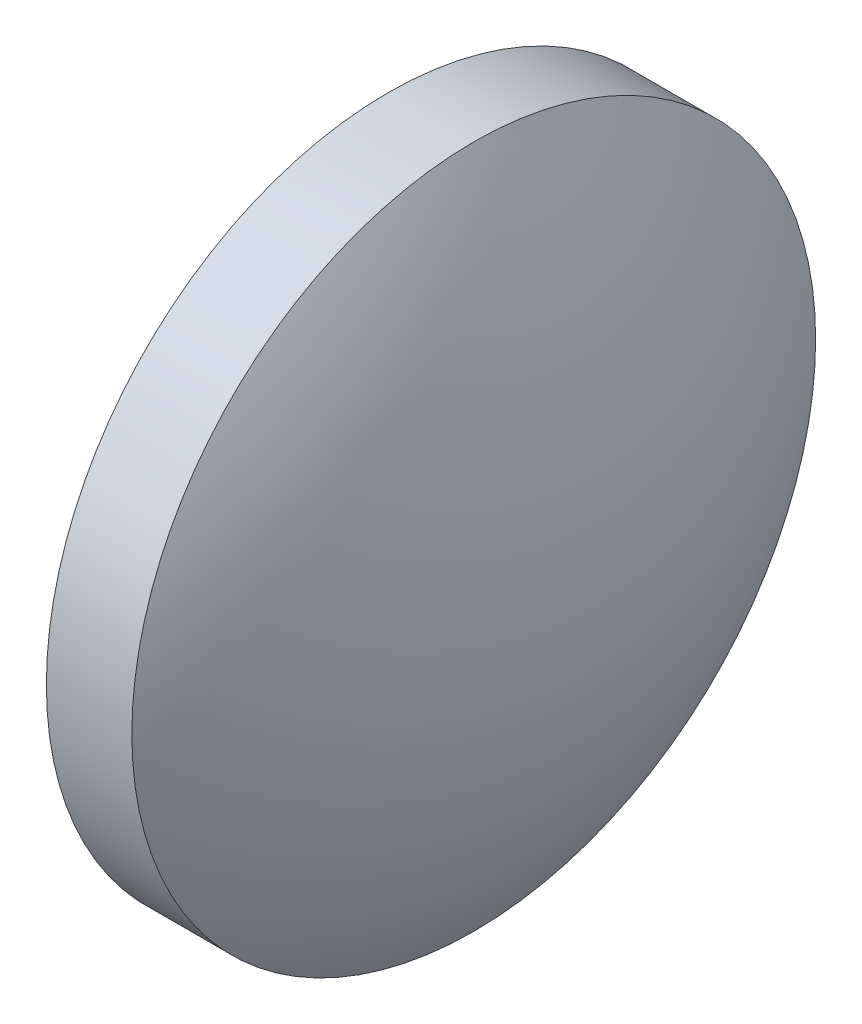
SolidWorks part; units mm, degrees
ref_plane "前视基准面" through (0, 0, 0) normal (0, 0, 1) x (1, 0, 0)
ref_plane "上视基准面" through (0, 0, 0) normal (0, 1, 0) x (1, 0, 0)
ref_plane "右视基准面" through (0, 0, 0) normal (1, 0, 0) x (0, 0, -1)
sketch "草图1" plane through (0, 0, 0) normal (0, 0, 1) x (1, 0, 0)
  line L0 (53.4619, 38.6243) -> (55.4619, 38.6243)
  line L1 (55.4619, 38.6243) -> (55.4619, 22.6243)
  line L2 (55.4619, 22.6243) -> (53.4619, 22.6243)
  line L3 (53.4619, 22.6243) -> (53.4619, 38.6243)
  line L4 (49.5765, 30.6243) -> (58.6187, 30.6243) construction
  arc A0 (53.4619, 38.6243) -> (53.4619, 22.6243) centre (66.5251, 30.6243) ccw
  arc A1 (55.4619, 22.6243) -> (55.4619, 38.6243) centre (42.3986, 30.6243) ccw
  dimension "D1" = 2
  dimension "D2" = 16
revolve "旋转1" add sketch "草图1" angle 360 about L4
